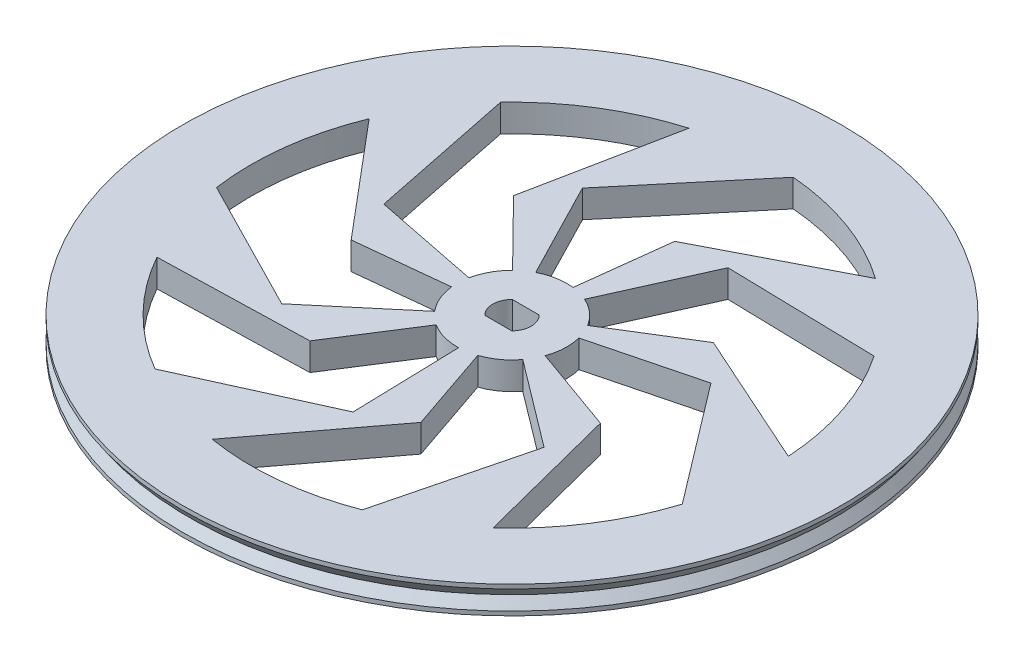
SolidWorks part; units mm, degrees
ref_plane "Front Plane" through (0, 0, 0) normal (0, 0, 1) x (1, 0, 0)
ref_plane "Top Plane" through (0, 0, 0) normal (0, 1, 0) x (1, 0, 0)
ref_plane "Right Plane" through (0, 0, 0) normal (1, 0, 0) x (0, 0, -1)
sketch "Sketch1" plane through (0, 0, 0) normal (1, 0, 0) x (0, 0, -1)
  line L0 (76.2, 0) -> (74.6745, 0)
  line L1 (0, -3.175) -> (76.2, -3.175)
  line L2 (0, -3.175) -> (0, 3.175)
  line L3 (0, 3.175) -> (76.2, 3.175)
  line L4 (76.2, -3.175) -> (76.2, -2.2108)
  line L5 (74.6745, 0) -> (76.2, 2.2108)
  line L6 (74.6745, 0) -> (76.2, -2.2108)
  line L7 (76.2, 2.2108) -> (76.2, 3.175)
  line L8 (76.2, 2.2108) -> (76.2, 0) construction
  line L9 (76.2, 0) -> (76.2, -2.2108) construction
  point P4 (0, 0)
  point P9 (76.2, -2.2108)
  dimension "D1" = 6.35
  dimension "D2" = 76.2
revolve "Revolve1" add sketch "Sketch1" angle 360 about L2
sketch "Sketch2" plane through (0, 3.175, 0) normal (0, 1, 0) x (1, 0, 0)
  line L0 (-3.1109, 3.175) -> (3.1109, 3.175)
  line L1 (3.1109, -3.175) -> (-3.1109, -3.175)
  line L2 (0, 3.175) -> (0, 0) construction
  line L3 (0, 0) -> (0, -3.175) construction
  line L5 (-17.3027, 33.5896) -> (4.896, 60.126)
  line L7 (34.6676, 49.3686) -> (4.0359, 33.5896)
  line L8 (4.0359, 33.5896) -> (1.5151, 12.6093)
  line L9 (15.4733, 34.4706) -> (50.061, 33.6601)
  line L10 (-5.8158, 11.2901) -> (-17.3027, 33.5896)
  line L11 (60.2129, 3.6766) -> (28.7777, 17.7873)
  line L12 (28.7777, 17.7873) -> (10.803, 6.6773)
  line L13 (5.2009, 11.5862) -> (15.4733, 34.4706)
  line L14 (36.5976, 9.3945) -> (57.529, -18.1525)
  line L15 (40.4166, -44.784) -> (31.8493, -11.4091)
  line L16 (31.8493, -11.4091) -> (11.956, -4.2829)
  line L17 (12.3012, 3.1577) -> (36.5976, 9.3945)
  line L18 (30.1632, -22.7558) -> (21.6765, -56.2959)
  line L19 (-9.8142, -59.5213) -> (10.9377, -32.0143)
  line L20 (10.9377, -32.0143) -> (4.106, -12.018)
  line L21 (10.1384, -7.6487) -> (30.1632, -22.7558)
  line L22 (1.0153, -37.7705) -> (-30.4988, -52.0473)
  line L23 (-52.6547, -29.4379) -> (-18.2102, -28.512)
  line L24 (-18.2102, -28.512) -> (-6.836, -10.7032)
  line L25 (0.3413, -12.6954) -> (1.0153, -37.7705)
  line L26 (-28.8972, -24.3433) -> (-59.708, -8.606)
  line L27 (-55.8451, 22.8129) -> (-33.6455, -3.5396)
  line L28 (-33.6455, -3.5396) -> (-12.6303, -1.3288)
  line L29 (-9.7129, -8.1823) -> (-28.8972, -24.3433)
  line L30 (-37.0495, 7.4149) -> (-43.9558, 41.3158)
  line L31 (-16.983, 57.8851) -> (-23.745, 24.0982)
  line L32 (-23.745, 24.0982) -> (-8.9137, 9.0463)
  line L33 (-12.453, 2.4923) -> (-37.0495, 7.4149)
  arc A0 (-3.1109, 3.175) -> (-3.1109, -3.175) centre (0, 0) ccw
  arc A1 (3.1109, -3.175) -> (3.1109, 3.175) centre (0, 0) ccw
  arc A2 (1.5151, 12.6093) -> (-5.8158, 11.2901) centre (0, 0) ccw
  arc A3 (34.6676, 49.3686) -> (4.896, 60.126) centre (0, 0) ccw
  arc A4 (60.2129, 3.6766) -> (50.061, 33.6601) centre (0, 0) ccw
  arc A5 (10.803, 6.6773) -> (5.2009, 11.5862) centre (0, 0) ccw
  arc A6 (40.4166, -44.784) -> (57.529, -18.1525) centre (0, 0) ccw
  arc A7 (11.956, -4.2829) -> (12.3012, 3.1577) centre (0, 0) ccw
  arc A8 (-9.8142, -59.5213) -> (21.6765, -56.2959) centre (0, 0) ccw
  arc A9 (4.106, -12.018) -> (10.1384, -7.6487) centre (0, 0) ccw
  arc A10 (-52.6547, -29.4379) -> (-30.4988, -52.0473) centre (0, 0) ccw
  arc A11 (-6.836, -10.7032) -> (0.3413, -12.6954) centre (0, 0) ccw
  arc A12 (-55.8451, 22.8129) -> (-59.708, -8.606) centre (0, 0) ccw
  arc A13 (-12.6303, -1.3288) -> (-9.7129, -8.1823) centre (0, 0) ccw
  arc A14 (-16.983, 57.8851) -> (-43.9558, 41.3158) centre (0, 0) ccw
  arc A15 (-8.9137, 9.0463) -> (-12.453, 2.4923) centre (0, 0) ccw
  point P53 (0, 0)
  dimension "D2" = 8.89
  dimension "D3" = 25.4
  dimension "D4" = 120.65
  dimension "D1" = 6.35
  dimension "D5" = 7
extrude "Cut-Extrude1" cut sketch "Sketch2" against normal through all
